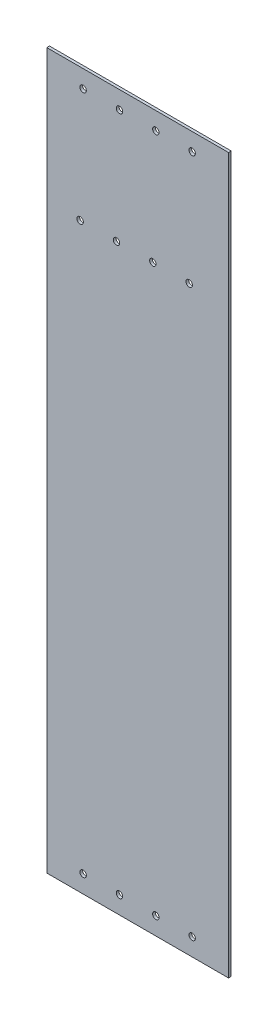
SolidWorks part; units mm, degrees
material "5052-H32"
ref_plane "Front Plane" through (0, 0, 0) normal (0, 0, 1) x (1, 0, 0)
ref_plane "Top Plane" through (0, 0, 0) normal (0, 1, 0) x (1, 0, 0)
ref_plane "Right Plane" through (0, 0, 0) normal (1, 0, 0) x (0, 0, -1)
sketch "Sketch1" plane through (0, 0, 0) normal (0, 0, 1) x (1, 0, 0)
  line L0 (55, 0) -> (-55, 0) construction
  line L1 (-77.5, 304.8) -> (77.5, 304.8)
  line L2 (-77.5, 304.8) -> (-77.5, -304.8)
  line L3 (-77.5, -304.8) -> (77.5, -304.8)
  line L4 (77.5, 304.8) -> (77.5, -304.8)
  line L5 (-77.5, 304.8) -> (77.5, -304.8) construction
  line L6 (-77.5, -304.8) -> (77.5, 304.8) construction
  point P0 (0, 0)
  point P20 (-46.5, 289.795)
  point P21 (-15.5, 289.795)
  point P23 (15.5, 289.795)
  point P24 (46.5, 289.795)
  point P33 (46.5, -289.795)
  point P34 (15.5, -289.795)
  point P35 (-15.5, -289.795)
  point P36 (-46.5, -289.795)
  dimension "D1" = 609.6
  dimension "D2" = 155
  dimension "D20" = 31
  dimension "D21" = 31
  dimension "D22" = 31
  dimension "D23" = 31
  dimension "D24" = 15.005
extrude "Boss-Extrude1" add sketch "Sketch1" along normal blind 2.305
hole_wizard "M5 Clearance Hole1" positions "Sketch2" profile "Sketch3" hole size "M5" standard "ANSI Metric" end condition through all
sketch "Sketch2" plane through (0, 0, 2.305) normal (0, 0, 1) x (1, 0, 0)
  point P0 (-46.5, 289.795)
  point P3 (-15.5, 289.795)
  point P6 (15.5, 289.795)
  point P9 (46.5, 289.795)
  point P12 (-46.5, -289.795)
  point P15 (-15.5, -289.795)
  point P18 (15.5, -289.795)
  point P21 (46.5, -289.795)
sketch "Sketch3" plane through (-46.5, 289.795, 2.305) normal (1, 0, 0) x (0, -1, 0)
  line L0 (0, 0) -> (0, 2.305)
  line L1 (0, 2.305) -> (2.75, 2.305)
  line L2 (2.75, 2.305) -> (2.75, 0)
  line L5 (2.75, 0) -> (0, 0)
  line L11 (0, -6.35) -> (0, 107.95) construction
  dimension "Thru Hole Dia." = 5.5
  dimension "Thru Hole Depth" = 2.305
sketch "Sketch4" plane through (0, 0, 2.305) normal (0, 0, 1) x (1, 0, 0)
  line L0 (-46.5, 289.795) -> (-46.5, 191.395) construction
  line L1 (-46.5, 191.395) -> (-49.04, 191.395) construction
  circle A0 centre (-49.04, 191.395) radius 2.75
  dimension "D3" = 5.5
  dimension "D1" = 2.54
  dimension "D2" = 98.4
extrude "Cut-Extrude1" cut sketch "Sketch4" against normal through all contours A0
pattern_linear "LPattern2" count 4 spacing 31 along (1, 0, 0) of "Cut-Extrude1"
